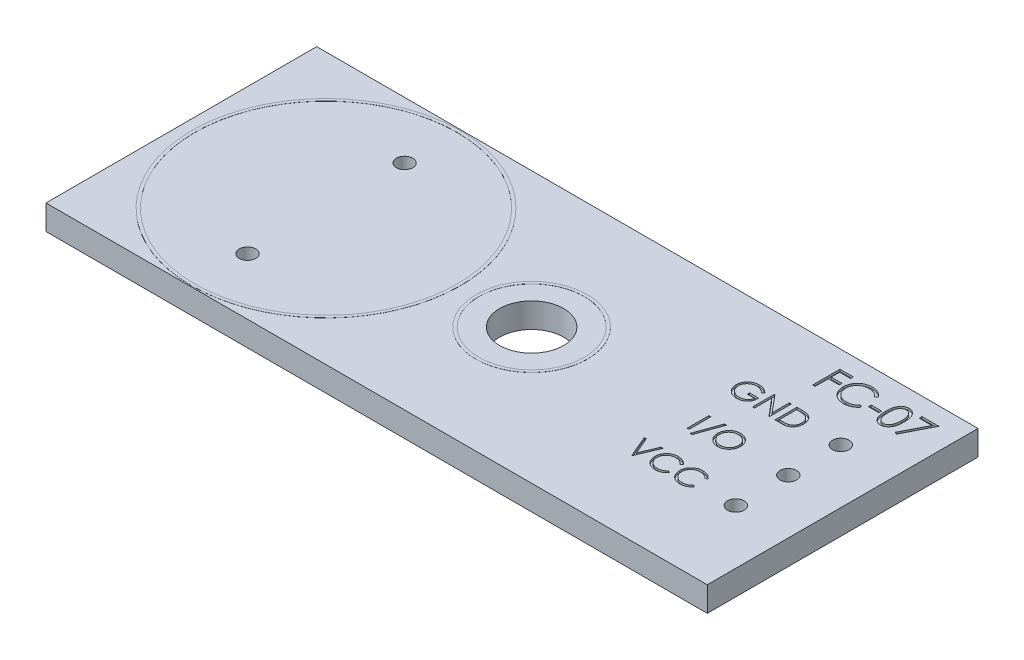
SolidWorks part; units mm, degrees
ref_plane "Front Plane" through (0, 0, 0) normal (0, 0, 1) x (1, 0, 0)
ref_plane "Top Plane" through (0, 0, 0) normal (0, 1, 0) x (1, 0, 0)
ref_plane "Right Plane" through (0, 0, 0) normal (1, 0, 0) x (0, 0, -1)
sketch "Sketch1" plane through (0, 0, 0) normal (0, 1, 0) x (1, 0, 0)
  line L1 (-16, 6.55) -> (16, 6.55)
  line L2 (-16, 6.55) -> (-16, -6.55)
  line L3 (-16, -6.55) -> (16, -6.55)
  line L4 (16, 6.55) -> (16, -6.55)
  line L5 (-16, 6.55) -> (16, -6.55) construction
  line L6 (-16, -6.55) -> (16, 6.55) construction
  point P0 (0, 0)
  dimension "D1" = 13.1
  dimension "D2" = 32
extrude "Boss-Extrude1" add sketch "Sketch1" along normal blind 1.2
sketch "Sketch2" plane through (0, 1.2, 0) normal (0, 1, 0) x (1, 0, 0)
  line L0 (0.95, 0) -> (16, 0) construction
  line L1 (16, -6.55) -> (16, 6.55) construction
  circle A0 centre (0.95, 0) radius 1.55
  dimension "D1" = 3.1
  dimension "D2" = 13.5
extrude "Cut-Extrude1" cut sketch "Sketch2" against normal up to next
sketch "Sketch4" plane through (0, 1.2, 0) normal (0, 1, 0) x (1, 0, 0)
  line L0 (13.37, -2.54) -> (13.37, 0) construction
  line L1 (13.37, 0) -> (13.37, 2.54) construction
  line L2 (13.37, 0) -> (16, 0) construction
  line L3 (16, -6.55) -> (16, 6.55) construction
  circle A0 centre (13.37, 0) radius 0.4
  circle A1 centre (13.37, 2.54) radius 0.4
  circle A2 centre (13.37, -2.54) radius 0.4
  dimension "D1" = 0.8
  dimension "D2" = 2.54
  dimension "D3" = 2.63
extrude "Cut-Extrude2" cut sketch "Sketch4" against normal up to next
sketch "Sketch5" plane through (0, 1.2, 0) normal (0, 1, 0) x (1, 0, 0)
  line L0 (-9, -3.8) -> (-9, 3.8) construction
  line L1 (-9, 0) -> (0, 0) construction
  circle A0 centre (-9, -3.8) radius 0.4
  circle A1 centre (-9, 3.8) radius 0.4
  dimension "D2" = 0.8
  dimension "D1" = 7.6
  dimension "D3" = 9
extrude "Cut-Extrude3" cut sketch "Sketch5" against normal up to next
sketch "Sketch6" plane through (0, 1.2, 0) normal (0, 1, 0) x (1, 0, 0)
  line L0 (7.9604, 1.9986) -> (11.9533, 1.9986) construction
  line L1 (7.9604, -0.4825) -> (11.9533, -0.4825) construction
  line L2 (7.9604, -2.9637) -> (11.9533, -2.9637) construction
  line L3 (9.9568, 1.9986) -> (9.9568, -0.4825) construction
  line L4 (9.9568, -0.4825) -> (9.9568, -2.9637) construction
  text T0 "GND" font "Century Gothic" height in points 4
  text T1 "I/O" font "Century Gothic" height in points 4
  text T2 "VCC" font "Century Gothic" height in points 4
extrude "Cut-Extrude4" cut sketch "Sketch6" against normal blind 0.1
sketch "Sketch7" plane through (0, 1.2, 0) normal (0, 1, 0) x (1, 0, 0)
  line L0 (9.6094, 4.3689) -> (15.429, 4.3689) construction
  text T0 "FC-07" font "Century Gothic" height in points 5
extrude "Cut-Extrude5" cut sketch "Sketch7" against normal blind 0.1
sketch "Sketch8" plane through (0, 1.2, 0) normal (0, 1, 0) x (1, 0, 0)
  line L0 (-9, 3.8) -> (-9, 0) construction
  line L1 (-9, 0) -> (-9, -3.8) construction
  circle A0 centre (-9, 0) radius 6.5
  circle A1 centre (-9, 0) radius 6.35
  circle A2 centre (0.95, 0) radius 2.7
  circle A3 centre (0.95, 0) radius 2.55
  dimension "D1" = 13
  dimension "D2" = 0.15
  dimension "D3" = 0.15
  dimension "D4" = 5.4
extrude "Boss-Extrude2" add sketch "Sketch8" along normal blind 0.005
